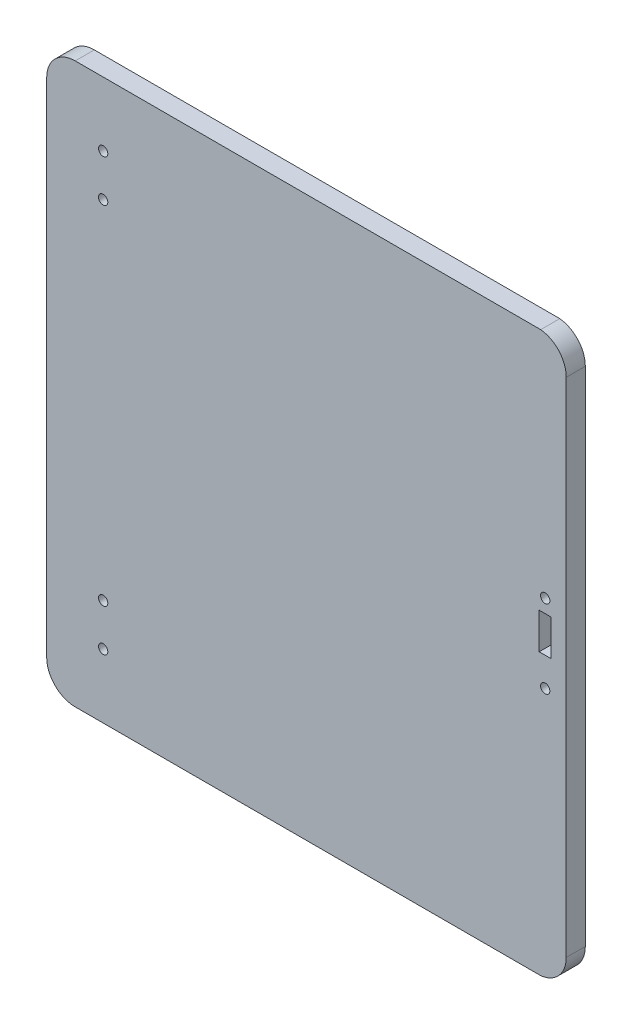
SolidWorks part; units mm, degrees
ref_plane "Front" through (0, 0, 0) normal (0, 0, 1) x (1, 0, 0)
ref_plane "Top" through (0, 0, 0) normal (0, 1, 0) x (1, 0, 0)
ref_plane "Right" through (0, 0, 0) normal (1, 0, 0) x (0, 0, -1)
sketch "Sketch2" plane through (0, 0, 0) normal (0, 0, 1) x (1, 0, 0)
  line L4 (77.5, 93.15) -> (-77.5, 93.15)
  line L5 (-87, 83.65) -> (-87, -83.65)
  line L6 (77.5, -93.15) -> (-77.5, -93.15)
  line L7 (86, 83.65) -> (86, -83.65)
  arc A4 (-77.5, 93.15) -> (-87, 83.65) centre (-77.5, 83.65) ccw
  arc A5 (-87, -83.65) -> (-77.5, -93.15) centre (-77.5, -83.65) ccw
  arc A6 (77.5, -93.15) -> (86, -83.65) centre (76.5001, -83.7028) ccw
  arc A7 (86, 83.65) -> (77.5, 93.15) centre (76.5001, 83.7028) ccw
  dimension "D1" = 173
  dimension "D2" = 186.3
extrude "Boss-Extrude1" add sketch "Sketch2" along normal blind 6.35
sketch "Sketch3" plane through (0, 0, 6.35) normal (0, 0, 1) x (1, 0, 0)
  line L1 (81, 0) -> (77, 0)
  line L2 (81, 0) -> (81, 12)
  line L3 (81, 12) -> (77, 12)
  line L4 (77, 0) -> (77, 12)
  line L5 (-87, 83.65) -> (-87, -83.65) construction
  dimension "D1" = 4
  dimension "D2" = 12
  dimension "D3" = 164
extrude "Cut-Extrude1" cut sketch "Sketch3" against normal blind 6.35
sketch "Sketch4" plane through (0, 0, 6.35) normal (0, 0, 1) x (1, 0, 0)
  line L0 (-87, 0) -> (86, 0) construction
  line L1 (-87, 83.65) -> (-87, -83.65) construction
  line L2 (86, -83.65) -> (86, 83.65) construction
  line L3 (-68.2, 71.8) -> (-68.2, 57.8) construction
  line L4 (-68.2, -71.8) -> (-68.2, -57.8) construction
  circle A0 centre (-68.2, 71.8) radius 1.55
  circle A1 centre (-68.2, 57.8) radius 1.55
  circle A2 centre (-68.2, -57.8) radius 1.55
  circle A3 centre (-68.2, -71.8) radius 1.55
  dimension "D1" = 3.1
  dimension "D2" = 18.8
  dimension "D3" = 71.8
  dimension "D4" = 14
extrude "Cut-Extrude2" cut sketch "Sketch4" against normal through all
sketch "Sketch5" plane through (0, 0, 6.35) normal (0, 0, 1) x (1, 0, 0)
  line L0 (81, 12) -> (77, 12) construction
  line L1 (77, 0) -> (81, 0) construction
  circle A0 centre (79, 16.45) radius 1.55
  circle A1 centre (79, -9.55) radius 1.55
  point P9 (79, 12)
  dimension "D1" = 3.1
  dimension "D2" = 4.45
  dimension "D3" = 9.55
extrude "Cut-Extrude3" cut sketch "Sketch5" against normal through all
